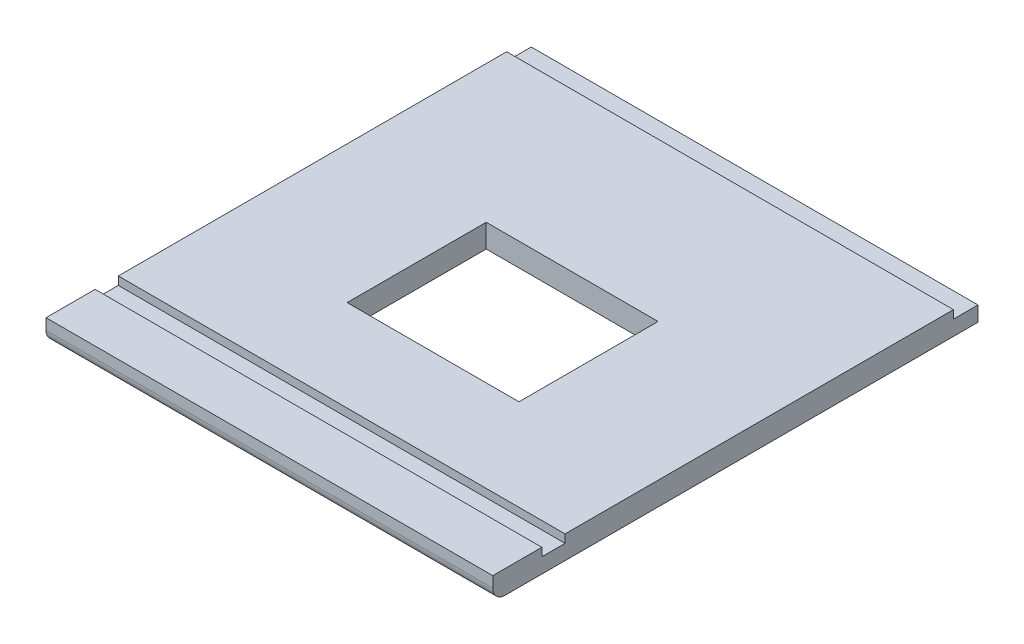
SolidWorks part; units mm, degrees
ref_plane "Front Plane" through (0, 0, 0) normal (0, 0, 1) x (1, 0, 0)
ref_plane "Top Plane" through (0, 0, 0) normal (0, 1, 0) x (1, 0, 0)
ref_plane "Right Plane" through (0, 0, 0) normal (1, 0, 0) x (0, 0, -1)
sketch "Sketch1" plane through (0, 0, 0) normal (0, 1, 0) x (1, 0, 0)
  line L1 (0, 0) -> (346.7, 0)
  line L2 (0, 0) -> (0, -376.55)
  line L3 (0, -376.55) -> (346.7, -376.55)
  line L4 (346.7, 0) -> (346.7, -376.55)
  dimension "D1" = 346.7
  dimension "D2" = 376.55
extrude "Boss-Extrude1" add sketch "Sketch1" along normal blind 18
sketch "Sketch2" plane through (0, 18, 0) normal (0, 1, 0) x (1, 0, 0)
  line L0 (0, -376.55) -> (346.7, -376.55) construction
  line L1 (346.7, -338.45) -> (0, -338.45)
  line L2 (346.7, -338.45) -> (346.7, -320.45)
  line L3 (346.7, -320.45) -> (0, -320.45)
  line L4 (0, -338.45) -> (0, -320.45)
  line L5 (0, 0) -> (0, -376.55) construction
  line L6 (346.7, -376.55) -> (346.7, 0) construction
  dimension "D1" = 18
  dimension "D2" = 38.1
  dimension "D3" = 0
  dimension "D4" = 0
extrude "Cut-Extrude1" cut sketch "Sketch2" against normal blind 6.35
sketch "Sketch3" plane through (0, 18, 0) normal (0, 1, 0) x (1, 0, 0)
  line L0 (0, -376.55) -> (346.7, -376.55) construction
  line L1 (106.675, -249.55) -> (240.025, -249.55)
  line L2 (106.675, -249.55) -> (106.675, -141.6)
  line L3 (106.675, -141.6) -> (240.025, -141.6)
  line L4 (240.025, -249.55) -> (240.025, -141.6)
  point P7 (173.35, -249.55)
  point P8 (173.35, -376.55)
  point P9 (106.675, -195.575)
  dimension "D1" = 107.95
  dimension "D2" = 133.35
  dimension "D3" = 0
  dimension "D4" = 180.975
extrude "Cut-Extrude3" cut sketch "Sketch3" against normal through all
fillet "Fillet1" radius 9.525 1 edges at (173.35, 0, 376.55)
sketch "Sketch6" plane through (0, 18, 0) normal (0, 1, 0) x (1, 0, 0)
  line L0 (346.7, -320.45) -> (346.7, 0) construction
  line L1 (0, 0) -> (346.7, 0)
  line L2 (0, 0) -> (0, -19.05)
  line L3 (0, -19.05) -> (346.7, -19.05)
  line L4 (346.7, 0) -> (346.7, -19.05)
  dimension "D1" = 19.05
extrude "Cut-Extrude4" cut sketch "Sketch6" against normal up to surface (6.35 mm away) up to face at (173.35, 11.65, 329.45)
sketch "Sketch7" [suppressed] plane through (0, 18, 0) normal (0, 1, 0) x (1, 0, 0)
  line L1 (0, -376.55) -> (346.7, -376.55)
  line L2 (0, -376.55) -> (0, -363.85)
  line L3 (0, -363.85) -> (346.7, -363.85)
  line L4 (346.7, -376.55) -> (346.7, -363.85)
  dimension "D1" = 12.7
extrude "Cut-Extrude5" [suppressed] cut sketch "Sketch7" against normal through all
fillet "Fillet2" [suppressed] radius 9.525
sketch "Sketch8" [suppressed] plane through (0, 11.65, 0) normal (0, 1, 0) x (1, 0, 0)
  line L0 (173.35, 0) -> (173.35, -363.85) construction
  line L1 (0, 0) -> (346.7, 0) construction
  line L2 (346.7, -363.85) -> (0, -363.85) construction
  line L3 (25.4, 20.153) -> (25.4, -383.3098) construction
  line L4 (321.3, 20.153) -> (321.3, -383.3098) construction
  line L5 (0, -9.525) -> (413.1787, -9.525) construction
  line L6 (0, -329.45) -> (346.7, -329.45) construction
  line L7 (0, -320.45) -> (0, -338.45) construction
  line L8 (346.7, -338.45) -> (346.7, -320.45) construction
  line L10 (0, -19.05) -> (0, 0) construction
  line L11 (0, -19.05) -> (0, -320.45) construction
  circle A0 centre (173.35, -9.525) radius 1.7859
  circle A1 centre (173.35, -329.45) radius 1.7859
  circle A2 centre (25.4, -329.45) radius 1.7859
  circle A3 centre (321.3, -329.45) radius 1.7859
  circle A4 centre (321.3, -9.525) radius 1.7859
  circle A5 centre (25.4, -9.525) radius 1.7859
  dimension "D1" = 3.5719
  dimension "D2" = 25.4
extrude "Cut-Extrude6" [suppressed] cut sketch "Sketch8" against normal through all
